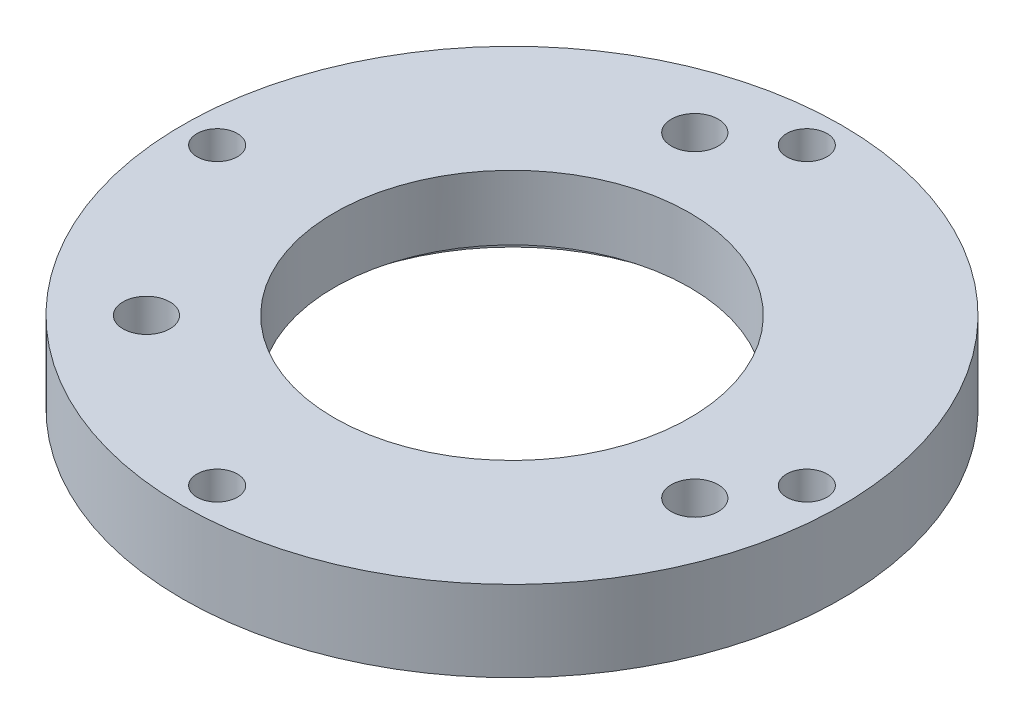
SolidWorks part; units mm, degrees
material "3.1355 (EN-AW 2024)"
ref_plane "Front" through (0, 0, 0) normal (0, 0, 1) x (1, 0, 0)
ref_plane "Top" through (0, 0, 0) normal (0, 1, 0) x (1, 0, 0)
ref_plane "Right" through (0, 0, 0) normal (1, 0, 0) x (0, 0, -1)
sketch "Эскиз1" plane through (0, 0, 0) normal (0, 1, 0) x (1, 0, 0)
  circle A0 centre (0, 0) radius 20.4
  circle A1 centre (0, 0) radius 11
  dimension "D1" = 40.8
  dimension "D2" = 22
extrude "Бобышка-Вытянуть1" add sketch "Эскиз1" along normal blind 5
sketch "Эскиз2" plane through (0, 5, 0) normal (0, 1, 0) x (1, 0, 0)
  circle A0 centre (0, 0) radius 18.25 construction
  point P3 (0, 18.25)
  point P4 (18.25, 0)
  point P5 (0, -18.25)
  point P6 (-18.25, 0)
  dimension "D1" = 36.5
hole_wizard "Отверстие обработанное метчиком M3x0.51" positions "Эскиз5" profile "Эскиз4" tap size "M3x0.5" standard "Ansi Metric" end condition through all
sketch "Эскиз5" plane through (0, 5, 0) normal (0, 1, 0) x (1, 0, 0)
  point P0 (-18.25, 0)
  point P3 (0, 18.25)
  point P6 (18.25, 0)
  point P9 (0, -18.25)
sketch "Эскиз4" plane through (-18.25, 5, 0) normal (1, 0, 0) x (0, 0, 1)
  line L0 (0, 0) -> (0, 5)
  line L1 (0, 5) -> (1.25, 5)
  line L2 (1.25, 5) -> (1.25, 0)
  line L5 (1.25, 0) -> (0, 0)
  line L11 (0, -6.35) -> (0, 107.95) construction
  dimension "Диаметр проходного сверла" = 2.5
  dimension "Глубина проходного сверла" = 5
cosmetic thread "Отверстие резьбы1" parameters "D2"=3
cosmetic thread "Отверстие резьбы2" parameters "D2"=3
cosmetic thread "Отверстие резьбы3" parameters "D2"=3
cosmetic thread "Отверстие резьбы4" parameters "D2"=3
sketch "Эскиз6" plane through (0, 0, 0) normal (0, -1, 0) x (1, 0, 0)
  line L0 (0, 0) -> (-4.1411, -15.4548) construction
  line L1 (0, 0) -> (-11.3137, 11.3137) construction
  line L2 (0, 0) -> (15.4548, 4.1411) construction
  line L3 (18.25, 0) -> (0, -18.25) construction
  circle A0 centre (0, 0) radius 16 construction
  point P11 (0, 0)
  dimension "D1" = 32
  dimension "D2" = 120
  dimension "D3" = 120
  dimension "D4" = 30
hole_wizard "Цековка для винта с внутренним шестигранником M2.51" positions "Эскиз8" profile "Эскиз7" counterbore size "M2.5" standard "Ansi Metric" end condition through all
sketch "Эскиз8" plane through (0, 0, 0) normal (0, -1, 0) x (-1, 0, 0)
  line L0 (0, 0) -> (11.3137, -11.3137) construction
  line L1 (0, 0) -> (-15.4548, -4.1411) construction
  line L2 (0, 0) -> (4.1411, 15.4548) construction
  circle A0 centre (0, 0) radius 16 construction
  point P0 (11.3137, -11.3137)
  point P9 (4.1411, 15.4548)
  point P12 (-15.4548, -4.1411)
sketch "Эскиз7" plane through (-11.3137, 0, 11.3137) normal (1, 0, 0) x (0, 0, -1)
  line L0 (0, 0) -> (0, 5)
  line L1 (0, 5) -> (1.45, 5)
  line L3 (1.45, 5) -> (1.45, 2.5)
  line L4 (1.45, 2.5) -> (2.75, 2.5)
  line L5 (2.75, 2.5) -> (2.75, 0)
  line L7 (2.75, 0) -> (0, 0)
  line L11 (0, -6.35) -> (0, 107.95) construction
  dimension "Диаметр сквозного отверстия" = 2.9
  dimension "Глубина сквозного отверстия" = 5
  dimension "Диаметр цековки" = 5.5
  dimension "Глубина цековки" = 2.5
sketch "Эскиз9" plane through (0, 0, 0) normal (0, -1, 0) x (1, 0, 0)
  circle A0 centre (0, 0) radius 12.25
  dimension "D1" = 24.5
extrude "Вырез-Вытянуть1" cut sketch "Эскиз9" against normal blind 1
fillet "Скругление1" [suppressed] radius 1
equation "\"D1@Эскиз2\"=36.5"
